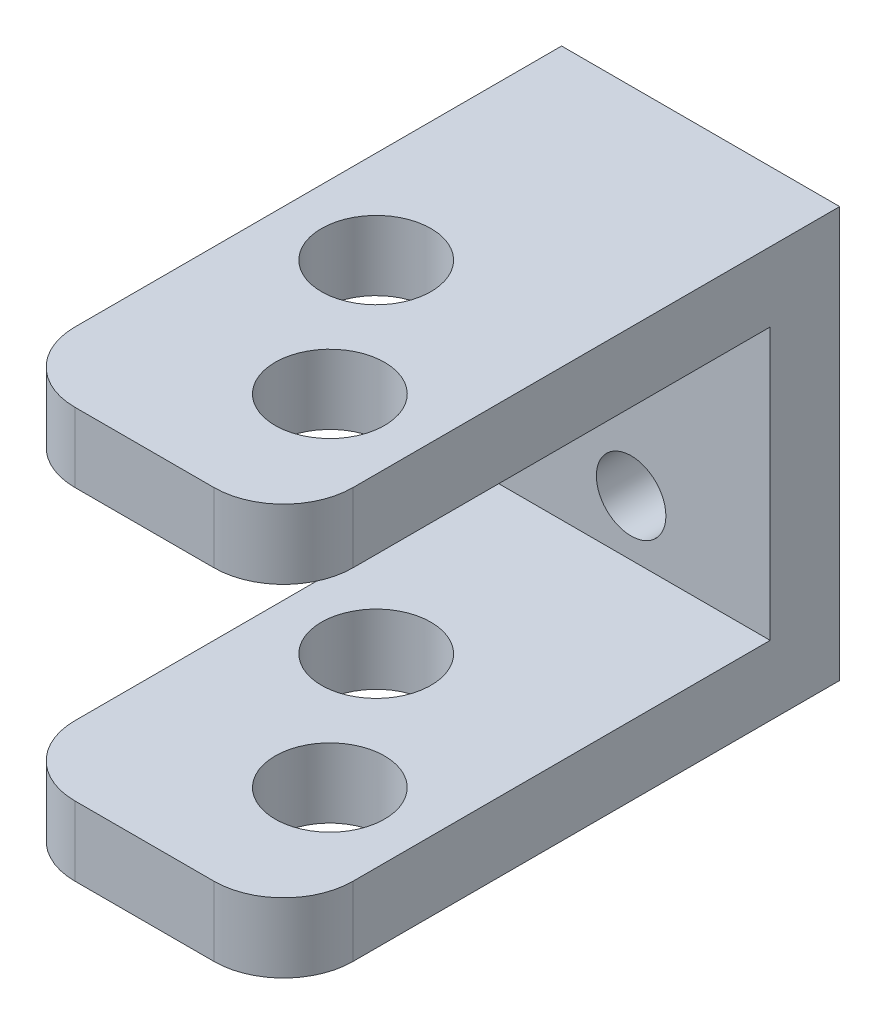
SolidWorks part; units mm, degrees
ref_plane "Front Plane" through (0, 0, 0) normal (0, 0, 1) x (1, 0, 0)
ref_plane "Top Plane" through (0, 0, 0) normal (0, 1, 0) x (1, 0, 0)
ref_plane "Right Plane" through (0, 0, 0) normal (1, 0, 0) x (0, 0, -1)
sketch "Sketch1" plane through (0, 0, 0) normal (0, 0, 1) x (1, 0, 0)
  line L0 (0, -736.6) -> (0, 0) construction
  line L1 (-25.4, 0) -> (0, 0)
  line L2 (-25.4, 0) -> (-25.4, -37.4882)
  line L3 (-25.4, -37.4882) -> (0, -37.4882)
  line L4 (0, 0) -> (0, -37.4882)
  line L8 (-20.5345, -30.963) -> (-4.0245, -30.963) construction
  line L10 (0, 0) -> (-25.4, 0)
  line L11 (0, 0) -> (0, -6.35)
  line L12 (0, -6.35) -> (-25.4, -6.35)
  line L13 (-25.4, 0) -> (-25.4, -6.35)
  line L14 (-25.4, -37.4882) -> (0, -37.4882)
  line L15 (-25.4, -37.4882) -> (-25.4, -31.1382)
  line L16 (-25.4, -31.1382) -> (0, -31.1382)
  line L17 (0, -37.4882) -> (0, -31.1382)
  dimension "D1" = 6.5253
  dimension "D2" = 6.35
  dimension "D3" = 6.35
extrude "Boss-Extrude1" add sketch "Sketch1" along normal blind 6.35 contours L16 L2 L3 L4 | L2 L16 L4 L12 | L12 L4 L1 L2
sketch "Sketch2" plane through (0, 0, 6.35) normal (0, 0, 1) x (1, 0, 0)
  line L0 (-25.4, 0) -> (-25.4, -37.4882) construction
  line L1 (0, 0) -> (-25.4, 0)
  line L2 (0, 0) -> (0, -6.35)
  line L3 (0, -6.35) -> (-25.4, -6.35)
  line L4 (-25.4, 0) -> (-25.4, -6.35)
  line L5 (0, 0) -> (0, -37.4882) construction
  line L6 (-25.4, -37.4882) -> (0, -37.4882)
  line L7 (-25.4, -37.4882) -> (-25.4, -31.1382)
  line L8 (-25.4, -31.1382) -> (0, -31.1382)
  line L9 (0, -37.4882) -> (0, -31.1382)
  dimension "D1" = 6.35
  dimension "D2" = 6.35
extrude "Boss-Extrude2" add sketch "Sketch2" along normal blind 44.45
sketch "Sketch3" plane through (0, 0, 6.35) normal (0, 0, 1) x (1, 0, 0)
  line L3 (-12.7, -6.35) -> (-12.7, -31.1382) construction
  line L6 (-25.4, -6.35) -> (0, -6.35) construction
  line L7 (0, -31.1382) -> (-25.4, -31.1382) construction
  circle A0 centre (-12.7, -26.0582) radius 3.175
  circle A1 centre (-12.7, -11.43) radius 3.175
  circle A2 centre (-12.7, -11.43) radius 5.5562
  circle A3 centre (-12.7, -26.0582) radius 5.5563
  dimension "D1" = 6.35
  dimension "D6" = 11.1125
  dimension "D7" = 11.1125
  dimension "D2" = 5.08
  dimension "D3" = 5.08
extrude "Cut-Extrude1" cut sketch "Sketch3" against normal blind 38.1 contours L3 A1 | A1 L3 | L3 A0 | A0 L3
sketch "Sketch6" plane through (0, 0, 0) normal (0, 1, 0) x (1, 0, 0)
  line L4 (0, 0) -> (-25.4, 0)
  line L5 (-25.4, 0) -> (-25.4, -44.45)
  line L6 (-19.05, -50.8) -> (-6.35, -50.8)
  line L7 (0, -44.45) -> (0, 0)
  line L8 (0, 0) -> (-25.4, 0)
  line L9 (-25.4, 0) -> (-25.4, -44.45)
  line L10 (-19.05, -50.8) -> (-6.35, -50.8)
  line L11 (0, -44.45) -> (0, 0)
  circle A0 centre (-8.4667, -38.1) radius 5
  circle A2 centre (-16.9333, -25.4) radius 5
  arc A7 (-25.4, -44.45) -> (-19.05, -50.8) centre (-19.05, -44.45) ccw
  arc A8 (-25.4, -44.45) -> (-19.05, -50.8) centre (-19.05, -44.45) ccw
  arc A9 (-6.35, -50.8) -> (0, -44.45) centre (-6.35, -44.45) ccw
  arc A10 (-6.35, -50.8) -> (0, -44.45) centre (-6.35, -44.45) ccw
  dimension "D1" = 10
  dimension "D3" = 25.4
  dimension "D4" = 8.4667
  dimension "D5" = 8.4667
  dimension "D6" = 12.7
  dimension "D2" = 0
extrude "Cut-Extrude2" cut sketch "Sketch6" against normal through all contours A2 | A0
fillet "Fillet1" radius 6.35 4 edges at (0, -34.3132, 50.8) (0, -3.175, 50.8) (-25.4, -34.3132, 50.8) (-25.4, -3.175, 50.8)
